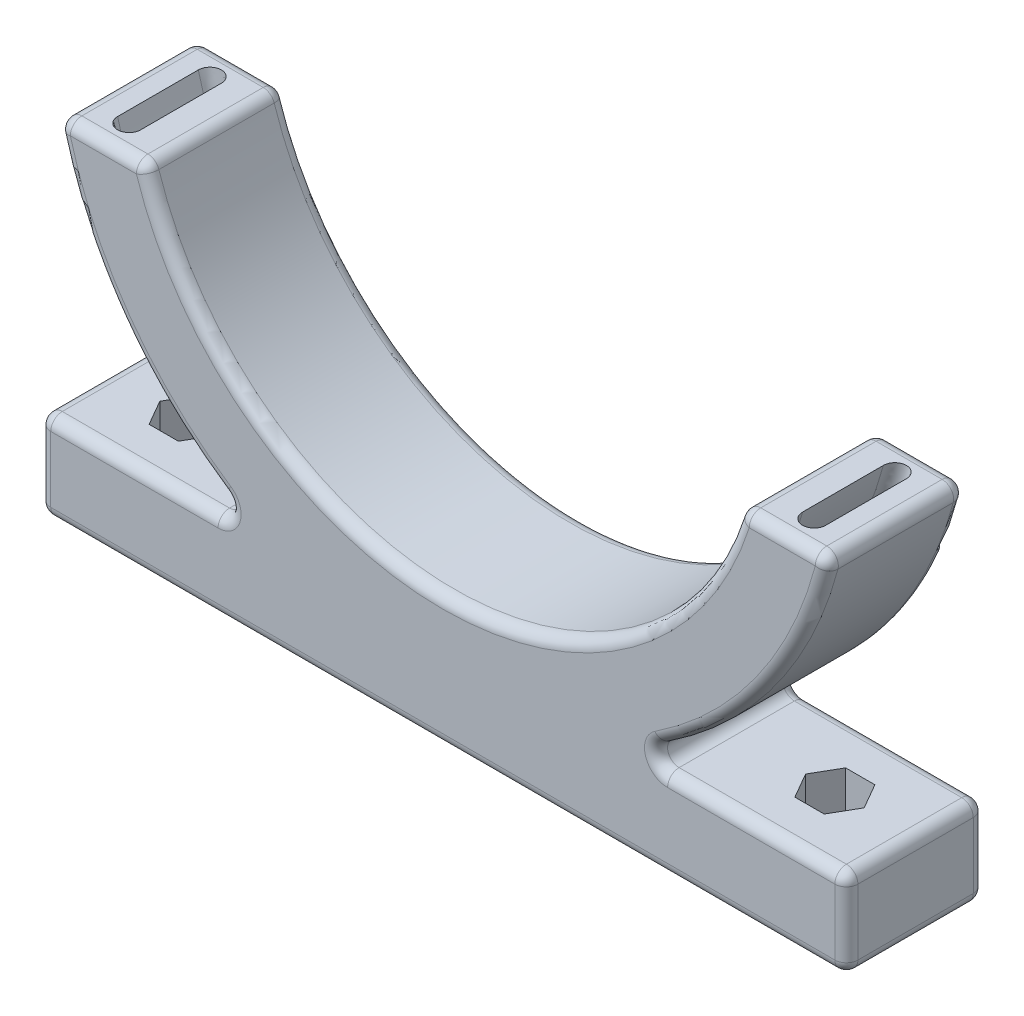
SolidWorks part; units mm, degrees
material "ABS"
ref_plane "Front Plane" through (0, 0, 0) normal (0, 0, 1) x (1, 0, 0)
ref_plane "Top Plane" through (0, 0, 0) normal (0, 1, 0) x (1, 0, 0)
ref_plane "Right Plane" through (0, 0, 0) normal (1, 0, 0) x (0, 0, -1)
sketch "Sketch1" plane through (0, 0, 0) normal (0, 0, 1) x (1, 0, 0)
  line L0 (-85.274, -19.05) -> (-65.6166, -19.05)
  line L1 (65.6166, -19.05) -> (85.274, -19.05)
  line L2 (40.1655, -77.597) -> (88.9, -77.597)
  line L3 (-88.9, -77.597) -> (-40.1655, -77.597)
  line L4 (-88.9, -77.597) -> (-88.9, -97.155)
  line L5 (-88.9, -97.155) -> (88.9, -97.155)
  line L6 (88.9, -77.597) -> (88.9, -97.155)
  line L7 (-88.9, -77.597) -> (88.9, -97.155) construction
  line L8 (-88.9, -97.155) -> (88.9, -77.597) construction
  arc A0 (-65.6166, -19.05) -> (65.6166, -19.05) centre (0, 0) ccw
  arc A1 (-85.274, -19.05) -> (85.274, -19.05) centre (0, 0) ccw
  point P3 (0, -87.376)
  dimension "D1" = 136.652
  dimension "D2" = 174.752
  dimension "D3" = 19.05
  dimension "D4" = 177.8
  dimension "D5" = 19.558
extrude "Boss-Extrude1" add sketch "Sketch1" along normal mid plane 30.48 contours L0 A1 L1 A0 | A1 L3 L4 L5 L6 L2
ref_point "Point1"
sketch "Sketch3" plane through (0, -19.05, 0) normal (0, 1, 0) x (1, 0, 0)
  line L0 (-75.4453, -8.89) -> (-75.4453, 8.89) construction
  line L1 (-77.9853, -8.89) -> (-77.9853, 8.89)
  line L2 (-72.9053, -8.89) -> (-72.9053, 8.89)
  arc A0 (-77.9853, -8.89) -> (-72.9053, -8.89) centre (-75.4453, -8.89) ccw
  arc A1 (-72.9053, 8.89) -> (-77.9853, 8.89) centre (-75.4453, 8.89) ccw
  point P2 (-75.4453, 0)
  dimension "D1" = 5.08
  dimension "D2" = 17.78
sketch "Sketch4" plane through (0, 0, 0) normal (0, 0, 1) x (1, 0, 0)
  circle A0 centre (0, 0) radius 77.978
  dimension "D1" = 155.956
sweep "Cut-Sweep1" cut profiles "Sketch3" path "Sketch4"
fillet "Fillet1" radius 2.54 30 edges at (-64.5328, -77.597, 15.24) (88.9, -77.597, 0) (64.5328, -77.597, 15.24) (40.1655, -77.597, 0) (64.5328, -77.597, -15.24) (88.9, -97.155, 0) (0, -97.155, 15.24) (0, -97.155, -15.24) (88.9, -87.376, 15.24) (88.9, -87.376, -15.24) (69.215, -53.3278, -15.24) (69.215, -53.3278, 15.24) (75.4453, -19.05, 15.24) (85.274, -19.05, 0) (75.4453, -19.05, -15.24) (65.6166, -19.05, 0) (0, -68.326, 15.24) (0, -68.326, -15.24) (-88.9, -97.155, 0) (-88.9, -87.376, 15.24) (-88.9, -87.376, -15.24) (-88.9, -77.597, 0) (-75.4453, -19.05, -15.24) (-65.6166, -19.05, 0) (-75.4453, -19.05, 15.24) (-85.274, -19.05, 0) (-40.1655, -77.597, 0) (-64.5328, -77.597, -15.24) (-69.215, -53.3278, -15.24) (-69.215, -53.3278, 15.24)
sketch "Sketch8" plane through (0, -77.597, 0) normal (0, 1, 0) x (1, 0, 0)
  line L0 (-44.8138, 0) -> (44.8138, 0) construction
  point P0 (-71.12, 0)
  point P1 (57.0468, 0)
  point P4 (71.12, 0)
  dimension "D1" = 71.12
  dimension "D2" = 71.12
sketch "Sketch5" plane through (0, -77.597, 0) normal (0, 1, 0) x (1, 0, 0)
  line L0 (-44.8138, 0) -> (44.8138, 0) construction
  line L2 (-67.8938, 5.588) -> (-74.3462, 5.588)
  line L3 (-74.3462, 5.588) -> (-77.5725, 0)
  line L4 (-77.5725, 0) -> (-74.3462, -5.588)
  line L5 (-74.3462, -5.588) -> (-67.8938, -5.588)
  line L6 (-67.8938, -5.588) -> (-64.6675, 0)
  line L7 (-64.6675, 0) -> (-67.8938, 5.588)
  line L8 (74.3462, 5.588) -> (67.8938, 5.588)
  line L9 (67.8938, 5.588) -> (64.6675, 0)
  line L10 (64.6675, 0) -> (67.8938, -5.588)
  line L11 (67.8938, -5.588) -> (74.3462, -5.588)
  line L12 (74.3462, -5.588) -> (77.5725, 0)
  line L13 (77.5725, 0) -> (74.3462, 5.588)
  circle A0 centre (-71.12, 0) radius 5.588 construction
  circle A1 centre (71.12, 0) radius 5.588 construction
  point P0 (-71.12, 0)
  point P1 (71.12, 0)
  dimension "D1" = 71.12
  dimension "D2" = 71.12
  dimension "D3" = 11.176
  dimension "D4" = 11.176
extrude "Cut-Extrude1" cut sketch "Sketch5" against normal blind 10.16
hole_wizard "H (0.266) Diameter Hole1" positions "3DSketch3" profile "Sketch9" hole size "H" standard "ANSI Inch"
sketch3d "3DSketch3"
  point P0 (-71.12, -77.597, 0)
  point P3 (71.12, -77.597, 0)
sketch "Sketch9" plane through (-71.12, -77.597, 0) normal (1, 0, 0) x (0, 0, 1)
  line L0 (0, 0) -> (0, 19.558)
  line L1 (0, 19.558) -> (3.3782, 19.558)
  line L2 (3.3782, 19.558) -> (3.3782, 0)
  line L5 (3.3782, 0) -> (0, 0)
  line L11 (0, -6.35) -> (0, 107.95) construction
  dimension "Thru Hole Dia." = 6.7564
  dimension "Thru Hole Depth" = 19.558
